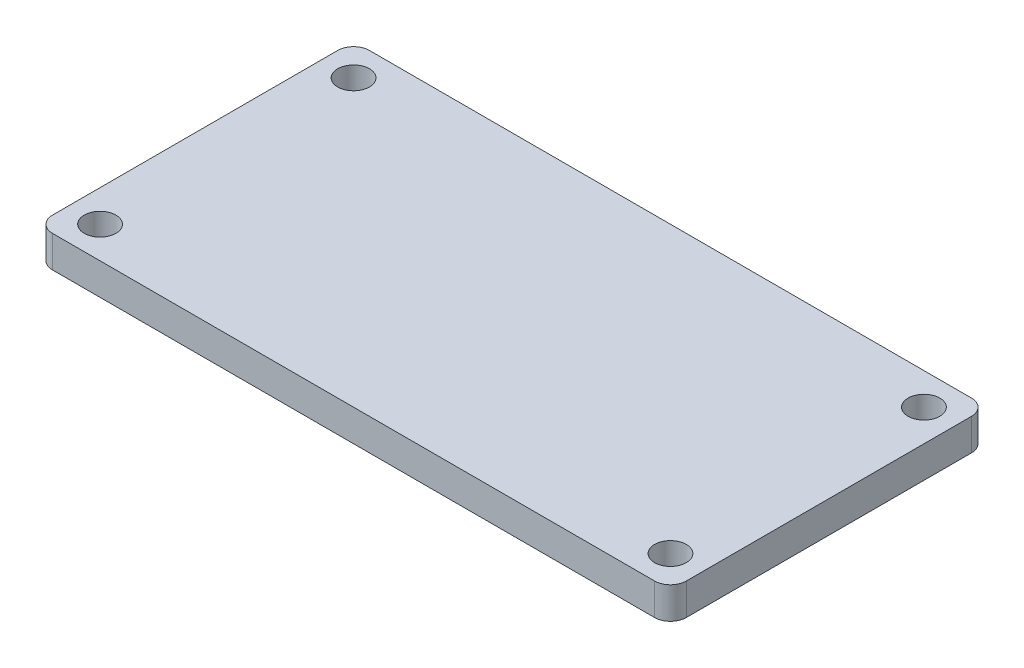
SolidWorks part; units mm, degrees
ref_plane "Front Plane" through (0, 0, 0) normal (0, 0, 1) x (1, 0, 0)
ref_plane "Top Plane" through (0, 0, 0) normal (0, 1, 0) x (1, 0, 0)
ref_plane "Right Plane" through (0, 0, 0) normal (1, 0, 0) x (0, 0, -1)
sketch "Sketch1" plane through (0, 0, 0) normal (0, 1, 0) x (1, 0, 0)
  line L0 (90.8921, 138.9693) -> (90.8921, 48.9693) construction
  line L5 (95.8921, 43.9693) -> (285.8921, 43.9693) construction
  line L6 (290.8921, 48.9693) -> (290.8921, 138.9693) construction
  line L7 (285.8921, 143.9693) -> (95.8921, 143.9693) construction
  line L8 (90.8921, 138.9693) -> (90.8921, 48.9693)
  line L9 (95.8921, 43.9693) -> (285.8921, 43.9693)
  line L10 (290.8921, 48.9693) -> (290.8921, 138.9693)
  line L11 (285.8921, 143.9693) -> (95.8921, 143.9693)
  arc A0 (95.8921, 143.9693) -> (90.8921, 138.9693) centre (95.8921, 138.9693) ccw construction
  arc A1 (90.8921, 48.9693) -> (95.8921, 43.9693) centre (95.8921, 48.9693) ccw construction
  arc A2 (285.8921, 43.9693) -> (290.8921, 48.9693) centre (285.8921, 48.9693) ccw construction
  arc A3 (290.8921, 138.9693) -> (285.8921, 143.9693) centre (285.8921, 138.9693) ccw construction
  arc A4 (95.8921, 143.9693) -> (90.8921, 138.9693) centre (95.8921, 138.9693) ccw
  arc A5 (90.8921, 48.9693) -> (95.8921, 43.9693) centre (95.8921, 48.9693) ccw
  arc A6 (285.8921, 43.9693) -> (290.8921, 48.9693) centre (285.8921, 48.9693) ccw
  arc A7 (290.8921, 138.9693) -> (285.8921, 143.9693) centre (285.8921, 138.9693) ccw
extrude "Boss-Extrude1" add sketch "Sketch1" along normal blind 10
sketch "Sketch2" plane through (0, 10, 0) normal (0, 1, 0) x (1, 0, 0)
  line L0 (90.8921, 138.9693) -> (90.8921, 48.9693) construction
  line L1 (290.8921, 48.9693) -> (290.8921, 138.9693) construction
  line L2 (285.8921, 143.9693) -> (95.8921, 143.9693) construction
  line L3 (95.8921, 43.9693) -> (285.8921, 43.9693) construction
  circle A0 centre (100.8921, 53.9693) radius 5
  circle A1 centre (100.8921, 133.9693) radius 5
  circle A2 centre (280.8921, 133.9693) radius 5
  circle A3 centre (280.8921, 53.9693) radius 5
  dimension "D1" = 10
  dimension "hole_hoz" = 10
  dimension "D2" = 10
  dimension "hole_vert" = 10
  dimension "D3" = 10
extrude "Cut-Extrude1" cut sketch "Sketch2" against normal through all
equation "\"D2@Sketch2\"=\"hole_hoz\""
equation "\"D3@Sketch2\"=\"hole_vert\""
